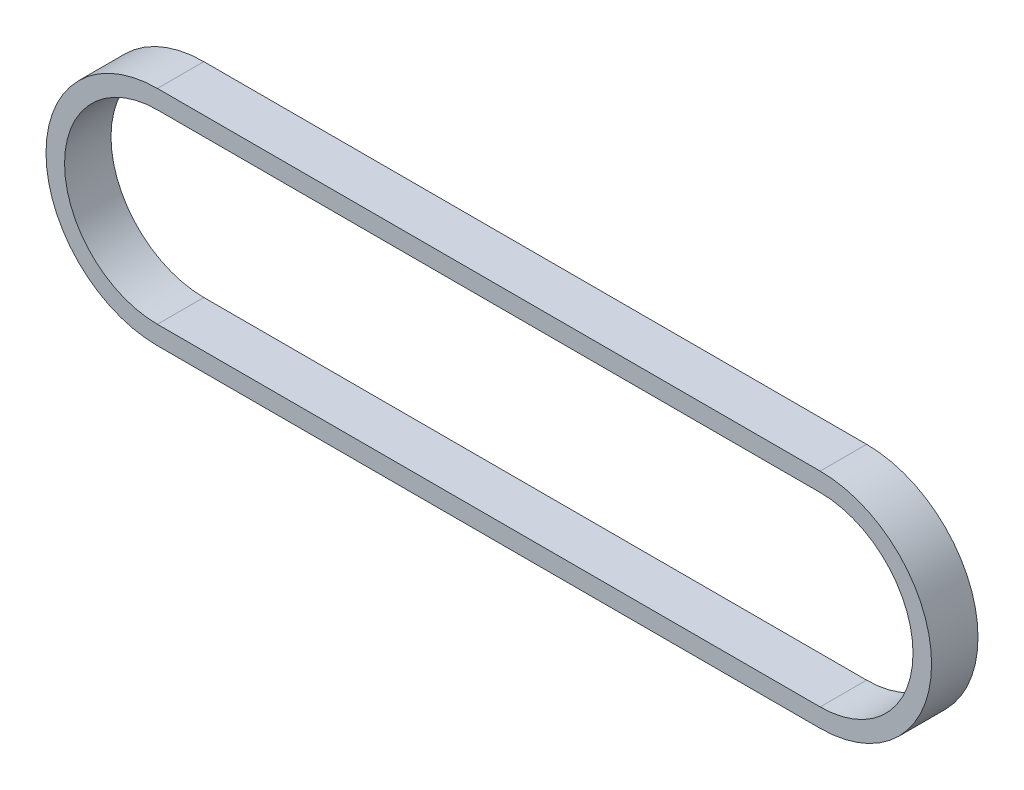
SolidWorks part; units mm, degrees
ref_plane "Front Plane" through (0, 0, 0) normal (0, 0, 1) x (1, 0, 0)
ref_plane "Top Plane" through (0, 0, 0) normal (0, 1, 0) x (1, 0, 0)
ref_plane "Right Plane" through (0, 0, 0) normal (1, 0, 0) x (0, 0, -1)
sketch "Sketch1" plane through (0, 0, 0) normal (0, 0, 1) x (1, 0, 0)
  line L0 (0, 0) -> (90.6615, 0) construction
  line L1 (0, 12.7) -> (90.6615, 12.7)
  line L2 (0, -12.7) -> (90.6615, -12.7)
  line L3 (0, 15.24) -> (90.6615, 15.24)
  line L4 (0, -15.24) -> (90.6615, -15.24)
  arc A0 (0, 12.7) -> (0, -12.7) centre (0, 0) ccw
  arc A1 (90.6615, -12.7) -> (90.6615, 12.7) centre (90.6615, 0) ccw
  arc A2 (90.6615, -15.24) -> (90.6615, 15.24) centre (90.6615, 0) ccw
  arc A3 (0, 15.24) -> (0, -15.24) centre (0, 0) ccw
  point P3 (45.3307, 0)
  dimension "D3" = 12.7
  dimension "D2" = 90.6615
  dimension "D1" = 2.54
extrude "Boss-Extrude1" add sketch "Sketch1" along normal blind 6.35
